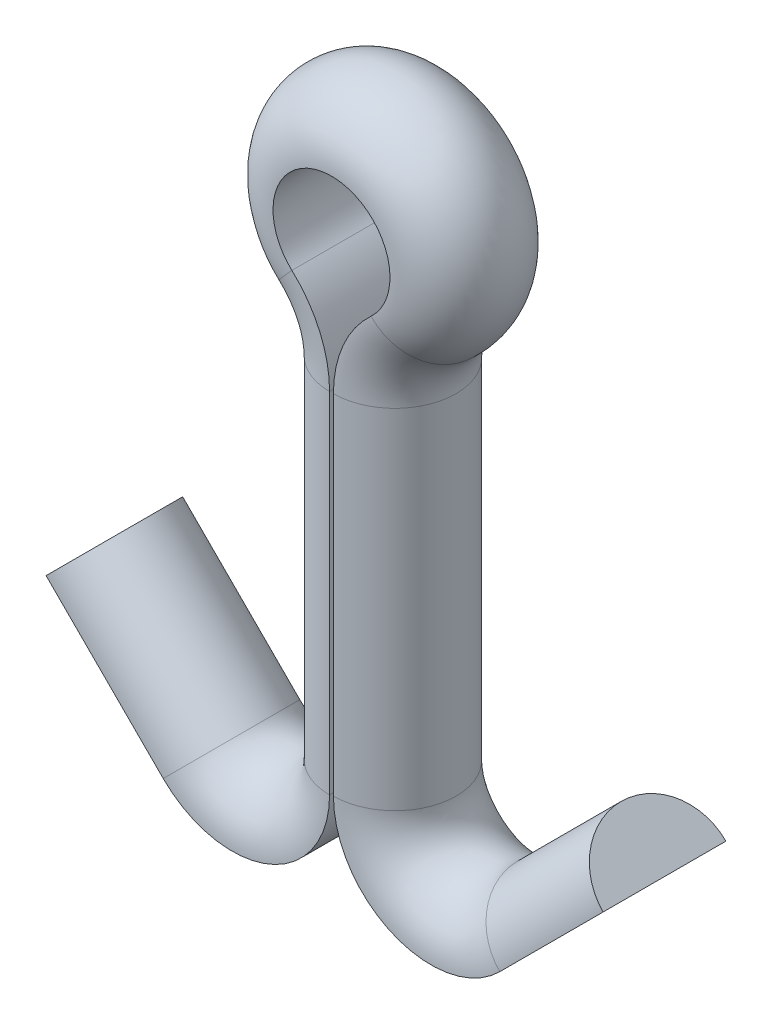
SolidWorks part; units mm, degrees
ref_plane "Top" through (0, 0, 0) normal (0, 0, 1) x (1, 0, 0)
ref_plane "Front" through (0, 0, 0) normal (0, 1, 0) x (1, 0, 0)
ref_plane "Right" through (0, 0, 0) normal (1, 0, 0) x (0, 0, -1)
sketch "Sketch1" plane through (0, 0, 0) normal (0, 0, 1) x (1, 0, 0)
  line L0 (0.025, -1.6812) -> (0.025, -6.223)
  line L1 (-0.025, -1.6812) -> (-0.025, -6.2357)
  line L2 (2.193, -7.121) -> (3.5401, -5.774) construction
  line L3 (-2.193, -7.1337) -> (-3.7197, -5.6071)
  arc A0 (-0.5163, -0.5604) -> (0.5163, -0.5604) centre (0, 0) cw
  arc A1 (-0.025, -1.6812) -> (-0.5163, -0.5604) centre (-1.549, -1.6812) ccw
  arc A2 (0.025, -1.6812) -> (0.5163, -0.5604) centre (1.549, -1.6812) cw
  arc A3 (0.025, -6.223) -> (2.193, -7.121) centre (1.295, -6.223) ccw construction
  arc A4 (-0.025, -6.2357) -> (-2.193, -7.1337) centre (-1.295, -6.2357) cw
  point P8 (-0.025, -0.7616)
  point P11 (0.025, -0.7616)
  dimension "D2" = 0.762
  dimension "D4" = 1.524
  dimension "D5" = 6.223
  dimension "D3" = 0.0127
  dimension "D6" = 1.27
  dimension "D1" = 0.05
  dimension "D7" = 2.159
  dimension "D8" = 1.905
  dimension "Bend Tip Angle" = 45
ref_plane "Plane4" through (0.025, -6.223, 0) normal (0, -1, 0) x (1, 0, 0)
sketch "Sketch2" plane through (0.025, -6.223, 0) normal (0, -1, 0) x (1, 0, 0)
  line L0 (0, 0.8001) -> (0, -0.8001)
  arc A0 (0, 0.8001) -> (0, -0.8001) centre (0, 0) cw
  dimension "D1" = 1.6002
sweep "Pin" add profiles "Sketch2" path "Sketch1"
sketch "Sketch3" plane through (0, 0, 0) normal (0, 0, 1) x (1, 0, 0)
  line L0 (2.193, -7.121) -> (3.5401, -5.774) construction
  line L1 (2.193, -7.121) -> (3.5401, -5.774)
  arc A0 (0.025, -6.223) -> (2.193, -7.121) centre (1.295, -6.223) ccw construction
  arc A1 (0.025, -6.223) -> (2.193, -7.121) centre (1.295, -6.223) ccw
sketch "Sketch4" plane through (0, -6.223, 0) normal (0, -1, 0) x (1, 0, 0)
  line L1 (0.025, 0.8001) -> (0.025, -0.8001)
  line L2 (0.025, 0.8001) -> (0.025, -0.8001)
  arc A1 (0.025, -0.8001) -> (0.025, 0.8001) centre (0.025, 0) ccw
  arc A2 (0.025, -0.8001) -> (0.025, 0.8001) centre (0.025, 0) ccw
  dimension "D1" = 0
sweep "Sweep1" add profiles "Sketch4" path "Sketch3"
